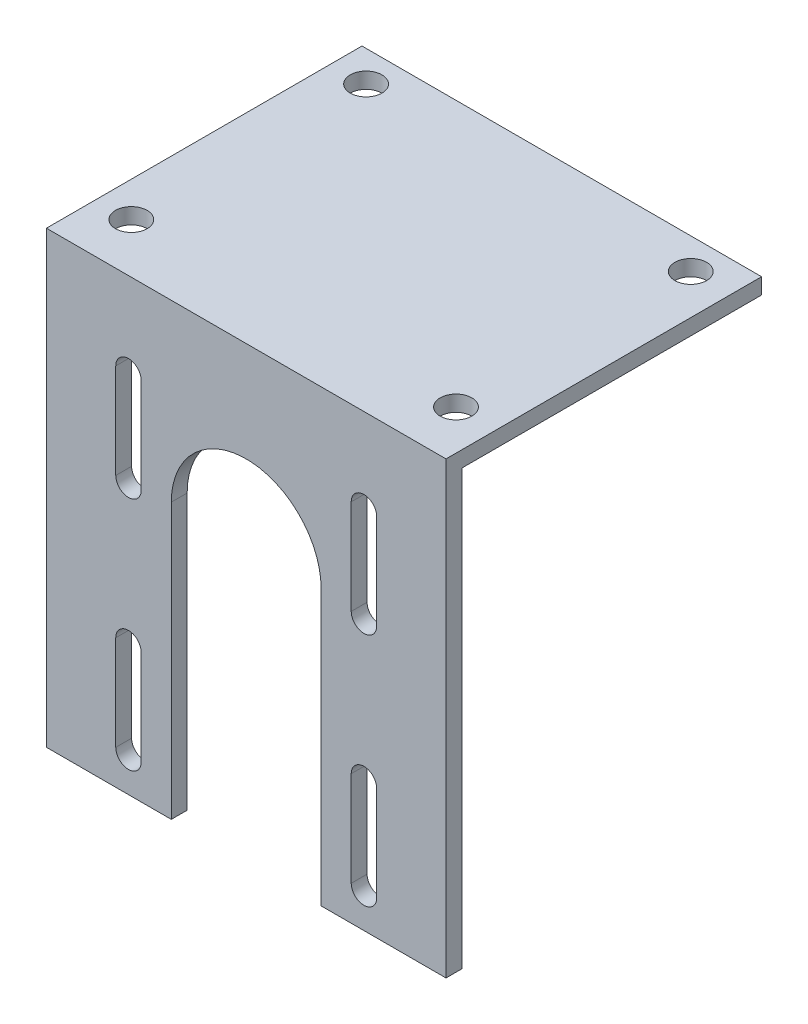
SolidWorks part; units mm, degrees
material "6061 Alloy"
ref_plane "Front Plane" through (0, 0, 0) normal (0, 0, 1) x (1, 0, 0)
ref_plane "Top Plane" through (0, 0, 0) normal (0, 1, 0) x (1, 0, 0)
ref_plane "Right Plane" through (0, 0, 0) normal (1, 0, 0) x (0, 0, -1)
sketch "Sketch1" plane through (0, 0, 0) normal (0, 0, 1) x (1, 0, 0)
  line L2 (0, 0) -> (0, -100)
  line L3 (0, -100) -> (80, -100)
  line L9 (80, -100) -> (80, 0)
  line L10 (0, 0) -> (80, 0)
  line L11 (16.43, -26.43) -> (63.57, -26.43) construction
  line L12 (40, 0) -> (40, -100) construction
  line L13 (0, -50) -> (80, -50) construction
  line L14 (16.43, -16.93) -> (16.43, -35.93) construction
  line L15 (63.57, -73.57) -> (63.57, -26.43) construction
  line L16 (18.98, -16.93) -> (18.98, -35.93)
  line L17 (13.88, -16.93) -> (13.88, -35.93)
  line L18 (63.57, -16.93) -> (63.57, -35.93) construction
  line L19 (61.02, -16.93) -> (61.02, -35.93)
  line L20 (66.12, -16.93) -> (66.12, -35.93)
  line L21 (16.43, -83.07) -> (16.43, -64.07) construction
  line L22 (18.98, -83.07) -> (18.98, -64.07)
  line L23 (13.88, -83.07) -> (13.88, -64.07)
  line L24 (63.57, -83.07) -> (63.57, -64.07) construction
  line L25 (61.02, -83.07) -> (61.02, -64.07)
  line L26 (66.12, -83.07) -> (66.12, -64.07)
  arc A8 (18.98, -16.93) -> (13.88, -16.93) centre (16.43, -16.93) ccw
  arc A9 (13.88, -35.93) -> (18.98, -35.93) centre (16.43, -35.93) ccw
  arc A10 (61.02, -16.93) -> (66.12, -16.93) centre (63.57, -16.93) cw
  arc A11 (66.12, -35.93) -> (61.02, -35.93) centre (63.57, -35.93) cw
  arc A12 (18.98, -83.07) -> (13.88, -83.07) centre (16.43, -83.07) cw
  arc A13 (13.88, -64.07) -> (18.98, -64.07) centre (16.43, -64.07) cw
  arc A14 (61.02, -83.07) -> (66.12, -83.07) centre (63.57, -83.07) ccw
  arc A15 (66.12, -64.07) -> (61.02, -64.07) centre (63.57, -64.07) ccw
  point P16 (40, -26.43)
  point P17 (63.57, -50)
  point P20 (16.43, -26.43)
  point P21 (80, -100)
  point P26 (0, 0)
  point P29 (80, 0)
  point P31 (63.57, -26.43)
  point P37 (16.43, -73.57)
  point P44 (63.57, -73.57)
  dimension "D3" = 47.14
  dimension "D4" = 47.14
  dimension "D6" = 19
  dimension "D5" = 2.55
  dimension "D1" = 80
  dimension "D2" = 100
extrude "Boss-Extrude1" add sketch "Sketch1" along normal blind 3.175
sketch "Sketch2" plane through (0, 0, 3.175) normal (0, 0, 1) x (1, 0, 0)
  line L0 (25, -35) -> (25, -100)
  line L1 (0, -100) -> (80, -100) construction
  line L2 (55, -35) -> (55, -100)
  line L3 (80, 0) -> (0, 0) construction
  line L8 (25, -100) -> (55, -100)
  arc A3 (25, -35) -> (55, -35) centre (40, -35) cw
  point P4 (40, 0)
  dimension "D1" = 15
  dimension "D2" = 35
extrude "Cut-Extrude2" cut sketch "Sketch2" against normal up to next
sketch "Sketch4" plane through (0, 0, 0) normal (0, 0, -1) x (-1, 0, 0)
  line L0 (0, 0) -> (0, -100) construction
  line L1 (-80, 0) -> (0, 0)
  line L2 (-80, 0) -> (-80, -3.175)
  line L3 (-80, -3.175) -> (0, -3.175)
  line L4 (0, 0) -> (0, -3.175)
  dimension "D1" = 3.175
extrude "Boss-Extrude2" add sketch "Sketch4" along normal blind 60
sketch "Sketch5" plane through (0, 0, 0) normal (0, 1, 0) x (1, 0, 0)
  line L0 (0, -3.175) -> (0, 60) construction
  line L1 (80, -3.175) -> (0, -3.175) construction
  circle A0 centre (7, 53.825) radius 3.175
  circle A1 centre (7, 6.825) radius 3.175
  circle A2 centre (72, 53.825) radius 3.175
  circle A3 centre (72, 6.825) radius 3.175
  dimension "D1" = 6.35
  dimension "D2" = 65
  dimension "D3" = 47
  dimension "D4" = 7
  dimension "D5" = 10
extrude "Cut-Extrude3" cut sketch "Sketch5" against normal up to surface (3.175 mm away) up to face at (40, -3.175, -30)
sketch "Sketch6" plane through (0, 0, 3.175) normal (0, 0, 1) x (1, 0, 0)
  line L5 (0, 0) -> (0, -100) construction
  line L6 (0, -90) -> (80, -90)
  line L7 (0, -90) -> (0, -100)
  line L8 (0, -100) -> (80, -100)
  line L9 (80, -90) -> (80, -100)
  dimension "D1" = 10
extrude "Cut-Extrude4" cut sketch "Sketch6" against normal through all
